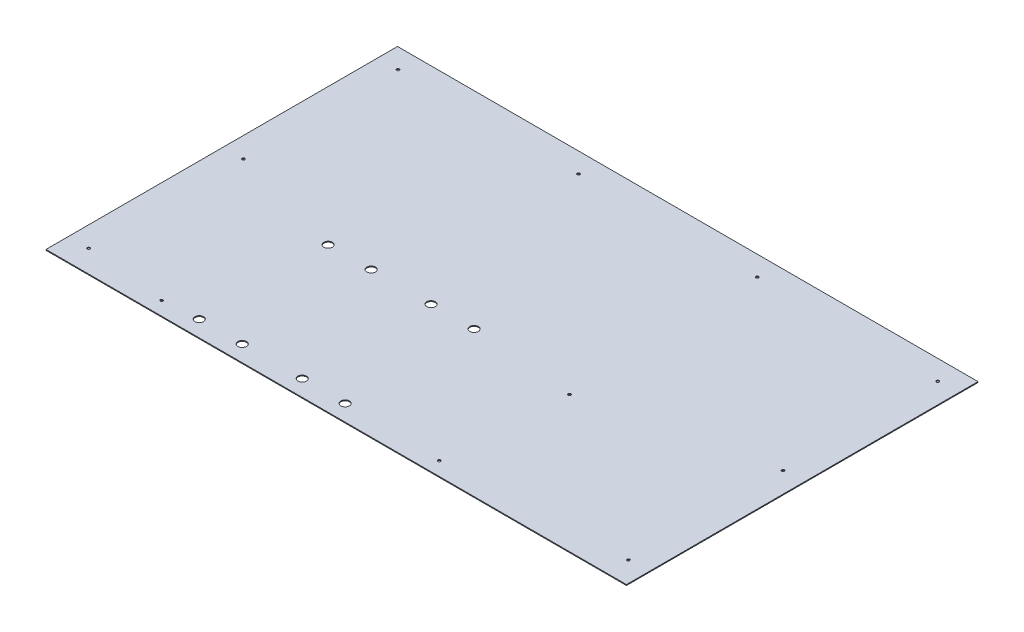
SolidWorks part; units mm, degrees
material "acero"
ref_plane "Alzado" through (0, 0, 0) normal (0, 0, 1) x (1, 0, 0)
ref_plane "Planta" through (0, 0, 0) normal (0, 1, 0) x (1, 0, 0)
ref_plane "Vista lateral" through (0, 0, 0) normal (1, 0, 0) x (0, 0, -1)
sketch "Croquis1" plane through (0, 0, 0) normal (0, 1, 0) x (1, 0, 0)
  line L1 (-337.7, -204.5) -> (337.7, -204.5)
  line L2 (-337.7, -204.5) -> (-337.7, 204.5)
  line L3 (-337.7, 204.5) -> (337.7, 204.5)
  line L4 (337.7, -204.5) -> (337.7, 204.5)
  line L5 (-337.7, -204.5) -> (337.7, 204.5) construction
  line L6 (-337.7, 204.5) -> (337.7, -204.5) construction
  point P0 (0, 0)
  dimension "D1" = 675.4
  dimension "D2" = 409
extrude "Saliente-Extruir1" add sketch "Croquis1" along normal blind 1
sketch "Croquis2" plane through (0, 0, 0) normal (0, -1, 0) x (1, 0, 0)
  line L0 (-337.7, 204.5) -> (337.7, 204.5) construction
  line L1 (337.7, 204.5) -> (337.7, -204.5) construction
  line L2 (0, 0) -> (0, -204.5) construction
  line L3 (337.7, -204.5) -> (-337.7, -204.5) construction
  circle A0 centre (-314, 178.6) radius 1.6
  circle A1 centre (-314, -181.4) radius 1.6
  circle A2 centre (314, -181.4) radius 1.6
  circle A3 centre (314, 178.6) radius 1.6
  circle A4 centre (113, 46.25) radius 1.6
  dimension "D1" = 3.2
  dimension "D2" = 158.25
  dimension "D5" = 360
  dimension "D3" = 224.7
  dimension "D4" = 628
  dimension "D7" = 25.9
extrude "Cortar-Extruir1" cut sketch "Croquis2" against normal up to next
sketch "Croquis3" plane through (0, 0, 0) normal (0, -1, 0) x (1, 0, 0)
  line L0 (-337.7, 204.5) -> (337.7, 204.5) construction
  line L1 (-337.7, -204.5) -> (-337.7, 204.5) construction
  line L2 (-93.4, 204.5) -> (-93.4, -9.8738) construction
  line L3 (-337.7, 204.5) -> (337.7, 204.5) construction
  circle A0 centre (-58.5, 35.6) radius 5
  circle A1 centre (-8.5, 35.6) radius 5
  circle A2 centre (-8.5, 185.6) radius 5
  circle A3 centre (-58.5, 185.6) radius 5
  circle A4 centre (-128.3, 185.6) radius 5
  circle A5 centre (-178.3, 185.6) radius 5
  circle A6 centre (-178.3, 35.6) radius 5
  circle A7 centre (-128.3, 35.6) radius 5
  dimension "D1" = 10
  dimension "D3" = 50
  dimension "D6" = 279.2
  dimension "D7" = 69.8
  dimension "D2" = 50
  dimension "D4" = 150
  dimension "D5" = 18.9
extrude "Cortar-Extruir2" cut sketch "Croquis3" against normal up to next
sketch "Croquis4" plane through (0, 0, 0) normal (0, -1, 0) x (1, 0, 0)
  line L0 (-314, -181.4) -> (314, -181.4) construction
  line L1 (314, -181.4) -> (314, 178.6) construction
  line L2 (314, 178.6) -> (-314, 178.6) construction
  line L3 (-314, 178.6) -> (-314, -181.4) construction
  line L4 (-337.7, -204.5) -> (-337.7, 204.5) construction
  circle A0 centre (-314, -1.4) radius 1.6
  circle A1 centre (314, -1.4) radius 1.6
  circle A2 centre (-219, 188.6) radius 1.6
  circle A3 centre (104, -181.4) radius 1.6
  circle A4 centre (113, 46.25) radius 1.6 construction
  circle A5 centre (104, 188.6) radius 1.6
  circle A6 centre (-104, -181.4) radius 1.6
  circle A7 centre (-314, -181.4) radius 1.6 construction
  point P12 (0, -181.4)
  point P13 (0, 178.6)
  dimension "D3" = 118.7
  dimension "D4" = 210
  dimension "D1" = 210
  dimension "D5" = 210
  dimension "D2" = 10
extrude "Cortar-Extruir3" cut sketch "Croquis4" against normal up to next
